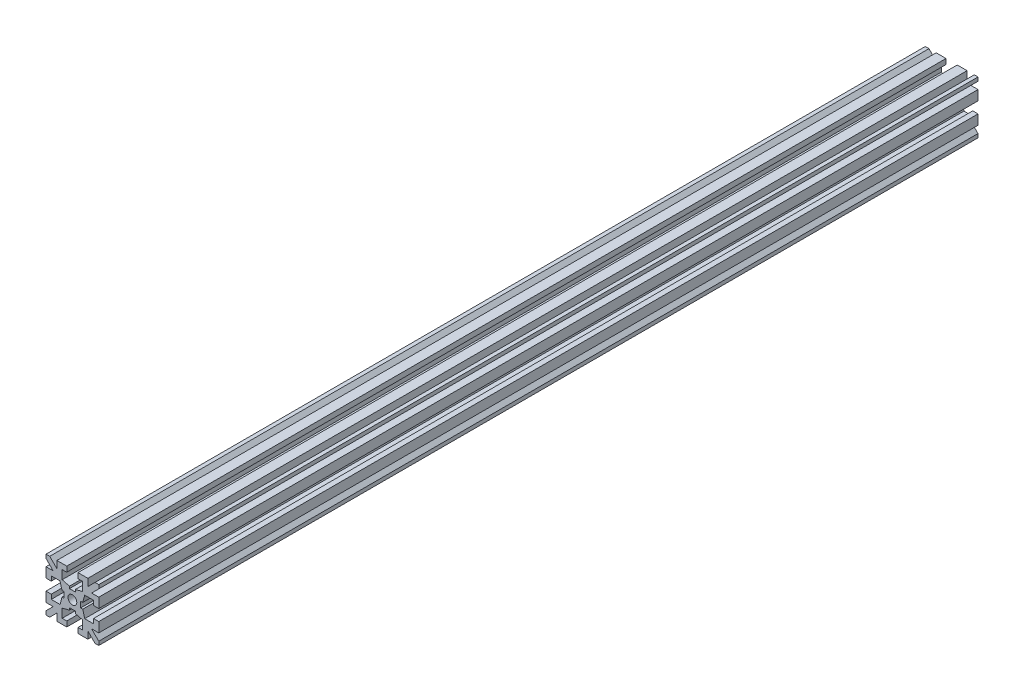
SolidWorks part; units mm, degrees
material "3.0205 (EN-AW 1200)"
ref_plane "Plano frontal" through (0, 0, 0) normal (0, 0, 1) x (1, 0, 0)
ref_plane "Plano superior" through (0, 0, 0) normal (0, 1, 0) x (1, 0, 0)
ref_plane "Plano direito" through (0, 0, 0) normal (1, 0, 0) x (0, 0, -1)
sketch "Esboço1" plane through (0, 0, 0) normal (0, 0, 1) x (1, 0, 0)
  line L0 (-25.7554, 0) -> (0, 0) construction
  line L1 (0, 0) -> (0, 21.5914) construction
  line L2 (0, 2.35) -> (-0.825, 2.35)
  line L3 (-0.825, 2.35) -> (-0.825, 2.95)
  line L4 (-0.825, 2.95) -> (-2.9, 3.5)
  line L5 (-2.9, 3.5) -> (-2.9, 6)
  line L6 (-2.9, 6) -> (-1.6, 6)
  line L7 (-1.6, 6) -> (-1.6, 7.5)
  line L8 (-1.6, 7.5) -> (-4.4, 7.5)
  line L9 (-4.4, 7.5) -> (-4.4, 5.4607)
  line L10 (-4.4, 5.4607) -> (-6.4393, 7.5)
  line L11 (-6.4393, 7.5) -> (-7.5, 7.5)
  line L12 (-7.5, 7.5) -> (0, 0) construction
  line L13 (-2.35, 0) -> (-2.35, 0.825)
  line L14 (-7.5, 6.4393) -> (-7.5, 7.5)
  line L15 (-5.4607, 4.4) -> (-7.5, 6.4393)
  line L16 (-7.5, 4.4) -> (-5.4607, 4.4)
  line L17 (-7.5, 1.6) -> (-7.5, 4.4)
  line L18 (-6, 1.6) -> (-7.5, 1.6)
  line L19 (-6, 2.9) -> (-6, 1.6)
  line L20 (-3.5, 2.9) -> (-6, 2.9)
  line L21 (-2.95, 0.825) -> (-3.5, 2.9)
  line L22 (-2.35, 0.825) -> (-2.95, 0.825)
  line L23 (-2.35, 0) -> (0, 0)
  line L24 (0, 0) -> (0, 2.35)
  dimension "D1" = 45
  dimension "D2" = 4.7
  dimension "D3" = 5.8
  dimension "D4" = 15
  dimension "D5" = 3.1
  dimension "D6" = 3.2
  dimension "D7" = 0.6
  dimension "D8" = 1.65
  dimension "D9" = 1.5
  dimension "D10" = 2.5
  dimension "D11" = 1.5
extrude "Ressalto-extrusão1" add sketch "Esboço1" along normal mid plane 250
mirror "Espelhar1" about plane through (0, 0, 0) normal (0, 1, 0) of "Ressalto-extrusão1"
mirror "Espelhar2" about plane through (0, 0, 0) normal (1, 0, 0) of "Espelhar1", "Ressalto-extrusão1"
sketch "Esboço2" plane through (0, 0, 125) normal (0, 0, 1) x (1, 0, 0)
  circle A0 centre (0, 0) radius 1.25
  dimension "D1" = 2.5
extrude "Corte-extrusão1" cut sketch "Esboço2" against normal through all both and the other way through all
